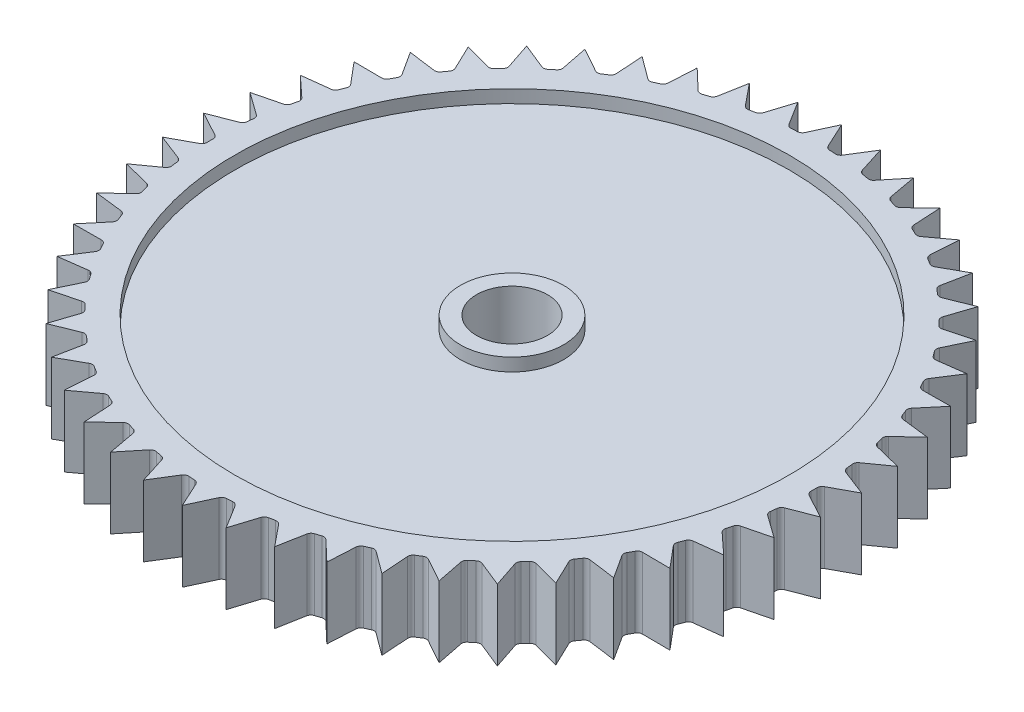
SolidWorks part; units mm, degrees
material "Acrylic (Medium-high impact)"
ref_plane "Front Plane" through (0, 0, 0) normal (0, 0, 1) x (1, 0, 0)
ref_plane "Top Plane" through (0, 0, 0) normal (0, 1, 0) x (1, 0, 0)
ref_plane "Right Plane" through (0, 0, 0) normal (1, 0, 0) x (0, 0, -1)
sketch "Sketch1" plane through (0, 0, 0) normal (0, 1, 0) x (1, 0, 0)
  line L0 (0, 0) -> (0, 28.57) construction
  line L1 (0, 0) -> (28.57, 0) construction
  line L2 (0, 0) -> (-28.57, 0) construction
  line L3 (0, 0) -> (0, -28.57) construction
  line L5 (0, 25.57) -> (-0.8983, 23.6239)
  line L7 (0, 25.57) -> (0.8983, 23.6239)
  line L12 (3.2048, 25.3684) -> (2.0696, 23.5502)
  line L13 (3.2048, 25.3684) -> (3.8521, 23.3251)
  line L14 (6.359, 24.7667) -> (5.0049, 23.1051)
  line L15 (6.359, 24.7667) -> (6.7451, 22.6583)
  line L16 (9.4129, 23.7744) -> (7.8613, 22.2957)
  line L17 (9.4129, 23.7744) -> (9.5318, 21.6343)
  line L18 (12.3184, 22.4072) -> (10.5937, 21.1346)
  line L19 (12.3184, 22.4072) -> (12.1681, 20.269)
  line L20 (15.0297, 20.6866) -> (13.1591, 19.6402)
  line L21 (15.0297, 20.6866) -> (14.6126, 18.5842)
  line L22 (17.5039, 18.6397) -> (15.5169, 17.836)
  line L23 (17.5039, 18.6397) -> (16.8265, 16.6062)
  line L24 (19.702, 16.2989) -> (17.63, 15.7506)
  line L25 (19.702, 16.2989) -> (18.7752, 14.3663)
  line L26 (21.5895, 13.7011) -> (19.465, 13.4168)
  line L27 (21.5895, 13.7011) -> (20.4277, 11.8999)
  line L28 (23.1364, 10.8872) -> (20.9931, 10.8714)
  line L29 (23.1364, 10.8872) -> (21.7581, 9.2458)
  line L30 (24.3185, 7.9016) -> (22.1901, 8.1545)
  line L31 (24.3185, 7.9016) -> (22.7453, 6.4459)
  line L33 (25.1171, 4.7913) -> (23.3738, 3.5443)
  line L34 (25.5195, 1.6056) -> (23.5209, 2.3799)
  line L35 (25.5195, 1.6056) -> (23.6337, 0.5868)
  line L36 (25.5195, -1.6056) -> (23.6337, -0.5868)
  line L37 (25.5195, -1.6056) -> (23.5209, -2.3799)
  line L38 (25.1171, -4.7913) -> (23.3738, -3.5443)
  line L39 (25.1171, -4.7913) -> (23.0372, -5.3091)
  line L40 (24.3185, -7.9016) -> (22.7453, -6.4459)
  line L41 (24.3185, -7.9016) -> (22.1901, -8.1545)
  line L42 (23.1364, -10.8872) -> (21.7581, -9.2458)
  line L43 (23.1364, -10.8872) -> (20.9931, -10.8714)
  line L44 (21.5895, -13.7011) -> (20.4277, -11.8999)
  line L45 (21.5895, -13.7011) -> (19.465, -13.4168)
  line L46 (19.702, -16.2989) -> (18.7752, -14.3663)
  line L47 (19.702, -16.2989) -> (17.63, -15.7506)
  line L48 (17.5039, -18.6397) -> (16.8265, -16.6062)
  line L49 (17.5039, -18.6397) -> (15.5169, -17.836)
  line L50 (15.0297, -20.6866) -> (14.6126, -18.5842)
  line L51 (15.0297, -20.6866) -> (13.1591, -19.6402)
  line L52 (12.3184, -22.4072) -> (12.1681, -20.269)
  line L53 (12.3184, -22.4072) -> (10.5937, -21.1346)
  line L54 (9.4129, -23.7744) -> (9.5318, -21.6343)
  line L55 (9.4129, -23.7744) -> (7.8613, -22.2957)
  line L56 (6.359, -24.7667) -> (6.7451, -22.6583)
  line L57 (6.359, -24.7667) -> (5.0049, -23.1051)
  line L58 (3.2048, -25.3684) -> (3.8521, -23.3251)
  line L59 (3.2048, -25.3684) -> (2.0696, -23.5502)
  line L60 (0, -25.57) -> (0.8983, -23.6239)
  line L61 (0, -25.57) -> (-0.8983, -23.6239)
  line L62 (-3.2048, -25.3684) -> (-2.0696, -23.5502)
  line L63 (-3.2048, -25.3684) -> (-3.8521, -23.3251)
  line L64 (-6.359, -24.7667) -> (-5.0049, -23.1051)
  line L65 (-6.359, -24.7667) -> (-6.7451, -22.6583)
  line L66 (-9.4129, -23.7744) -> (-7.8613, -22.2957)
  line L67 (-9.4129, -23.7744) -> (-9.5318, -21.6343)
  line L68 (-12.3184, -22.4072) -> (-10.5937, -21.1346)
  line L69 (-12.3184, -22.4072) -> (-12.1681, -20.269)
  line L70 (-15.0297, -20.6866) -> (-13.1591, -19.6402)
  line L71 (-15.0297, -20.6866) -> (-14.6126, -18.5842)
  line L72 (-17.5039, -18.6397) -> (-15.5169, -17.836)
  line L73 (-17.5039, -18.6397) -> (-16.8265, -16.6062)
  line L74 (-19.702, -16.2989) -> (-17.63, -15.7506)
  line L75 (-19.702, -16.2989) -> (-18.7752, -14.3663)
  line L76 (-21.5895, -13.7011) -> (-19.465, -13.4168)
  line L77 (-21.5895, -13.7011) -> (-20.4277, -11.8999)
  line L78 (-23.1364, -10.8872) -> (-20.9931, -10.8714)
  line L79 (-23.1364, -10.8872) -> (-21.7581, -9.2458)
  line L80 (-24.3185, -7.9016) -> (-22.1901, -8.1545)
  line L81 (-24.3185, -7.9016) -> (-22.7453, -6.4459)
  line L82 (-25.1171, -4.7913) -> (-23.0372, -5.3091)
  line L83 (-25.1171, -4.7913) -> (-23.3738, -3.5443)
  line L84 (-25.5195, -1.6056) -> (-23.5209, -2.3799)
  line L85 (-25.5195, -1.6056) -> (-23.6337, -0.5868)
  line L86 (-25.5195, 1.6056) -> (-23.6337, 0.5868)
  line L87 (-25.5195, 1.6056) -> (-23.5209, 2.3799)
  line L88 (-25.1171, 4.7913) -> (-23.3738, 3.5443)
  line L89 (-25.1171, 4.7913) -> (-23.0372, 5.3091)
  line L90 (-24.3185, 7.9016) -> (-22.7453, 6.4459)
  line L91 (-24.3185, 7.9016) -> (-22.1901, 8.1545)
  line L92 (-23.1364, 10.8872) -> (-21.7581, 9.2458)
  line L93 (-23.1364, 10.8872) -> (-20.9931, 10.8714)
  line L94 (-21.5895, 13.7011) -> (-20.4277, 11.8999)
  line L95 (-21.5895, 13.7011) -> (-19.465, 13.4168)
  line L96 (-19.702, 16.2989) -> (-18.7752, 14.3663)
  line L97 (-19.702, 16.2989) -> (-17.63, 15.7506)
  line L98 (-17.5039, 18.6397) -> (-16.8265, 16.6062)
  line L99 (-17.5039, 18.6397) -> (-15.5169, 17.836)
  line L100 (-15.0297, 20.6866) -> (-14.6126, 18.5842)
  line L101 (-15.0297, 20.6866) -> (-13.1591, 19.6402)
  line L102 (-12.3184, 22.4072) -> (-12.1681, 20.269)
  line L103 (-12.3184, 22.4072) -> (-10.5937, 21.1346)
  line L104 (-9.4129, 23.7744) -> (-9.5318, 21.6343)
  line L105 (-9.4129, 23.7744) -> (-7.8613, 22.2957)
  line L106 (-6.359, 24.7667) -> (-6.7451, 22.6583)
  line L107 (-6.359, 24.7667) -> (-5.0049, 23.1051)
  line L108 (-3.2048, 25.3684) -> (-3.8521, 23.3251)
  line L109 (-3.2048, 25.3684) -> (-2.0696, 23.5502)
  line L110 (25.1171, 4.7913) -> (23.0372, 5.3091) [skipped]
  line L111 (25.1171, 4.7913) -> (23.0372, 5.3091)
  arc A55 (-1.2403, 23.3921) -> (-1.7013, 23.3631) centre (0, 0) ccw
  circle A56 centre (0, 0) radius 25.57 construction
  arc A57 (0.8983, 23.6239) -> (1.2403, 23.3921) centre (1.2615, 23.7916) ccw
  arc A58 (-0.8983, 23.6239) -> (-1.2403, 23.3921) centre (-1.2615, 23.7916) cw
  arc A59 (2.0696, 23.5502) -> (1.7013, 23.3631) centre (1.7303, 23.7621) cw
  arc A60 (3.8521, 23.3251) -> (4.1623, 23.0522) centre (4.2334, 23.4459) ccw
  arc A61 (5.0049, 23.1051) -> (4.616, 22.9657) centre (4.6949, 23.3578) cw
  arc A62 (6.7451, 22.6583) -> (7.0187, 22.3488) centre (7.1386, 22.7304) ccw
  arc A63 (7.8613, 22.2957) -> (7.458, 22.2061) centre (7.5854, 22.5852) cw
  arc A64 (9.5318, 21.6343) -> (9.7644, 21.2929) centre (9.9312, 21.6565) ccw
  arc A65 (10.5937, 21.1346) -> (10.1824, 21.0962) centre (10.3562, 21.4564) cw
  arc A66 (12.1681, 20.269) -> (12.3561, 19.9012) centre (12.5671, 20.241) ccw
  arc A67 (13.1591, 19.6402) -> (12.7461, 19.6537) centre (12.9638, 19.9893) cw
  arc A68 (14.6126, 18.5842) -> (14.753, 18.1956) centre (15.0049, 18.5063) ccw
  arc A69 (15.5169, 17.836) -> (15.1089, 17.9012) centre (15.3669, 18.2069) cw
  arc A70 (16.8265, 16.6062) -> (16.9172, 16.2031) centre (17.206, 16.4798) ccw
  arc A71 (17.63, 15.7506) -> (17.2334, 15.8664) centre (17.5276, 16.1373) cw
  arc A72 (18.7752, 14.3663) -> (18.8146, 13.955) centre (19.1358, 14.1933) ccw
  arc A73 (19.465, 13.4168) -> (19.086, 13.5814) centre (19.412, 13.8133) cw
  arc A74 (20.4277, 11.8999) -> (20.4152, 11.4869) centre (20.7638, 11.6831) ccw
  arc A75 (20.9931, 10.8714) -> (20.6377, 11.0822) centre (20.9902, 11.2714) cw
  arc A76 (21.7581, 9.2458) -> (21.6939, 8.8376) centre (22.0644, 8.9885) ccw
  arc A77 (22.1901, 8.1545) -> (21.864, 8.4082) centre (22.2373, 8.5517) cw
  arc A78 (22.7453, 6.4459) -> (22.6305, 6.049) centre (23.017, 6.1523) ccw
  arc A79 (23.0372, 5.3091) -> (22.7454, 5.6016) centre (23.1338, 5.6972) cw
  arc A80 (23.3738, 3.5443) -> (23.2102, 3.1649) centre (23.6065, 3.219) ccw
  arc A81 (23.5209, 2.3799) -> (23.2681, 2.7067) centre (23.6654, 2.7529) cw
  arc A82 (23.6337, 0.5868) -> (23.4239, 0.2309) centre (23.8238, 0.2349) ccw
  arc A83 (23.6337, -0.5868) -> (23.4239, -0.2309) centre (23.8238, -0.2349) cw
  arc A84 (23.5209, -2.3799) -> (23.2681, -2.7067) centre (23.6654, -2.7529) ccw
  arc A85 (23.3738, -3.5443) -> (23.2102, -3.1649) centre (23.6065, -3.219) cw
  arc A86 (23.0372, -5.3091) -> (22.7454, -5.6016) centre (23.1338, -5.6972) ccw
  arc A87 (22.7453, -6.4459) -> (22.6305, -6.049) centre (23.017, -6.1523) cw
  arc A88 (22.1901, -8.1545) -> (21.864, -8.4082) centre (22.2373, -8.5517) ccw
  arc A89 (21.7581, -9.2458) -> (21.6939, -8.8376) centre (22.0644, -8.9885) cw
  arc A90 (20.9931, -10.8714) -> (20.6377, -11.0822) centre (20.9902, -11.2714) ccw
  arc A91 (20.4277, -11.8999) -> (20.4152, -11.4869) centre (20.7638, -11.6831) cw
  arc A92 (19.465, -13.4168) -> (19.086, -13.5814) centre (19.412, -13.8133) ccw
  arc A93 (18.7752, -14.3663) -> (18.8146, -13.955) centre (19.1358, -14.1933) cw
  arc A94 (17.63, -15.7506) -> (17.2334, -15.8664) centre (17.5276, -16.1373) ccw
  arc A95 (16.8265, -16.6062) -> (16.9172, -16.2031) centre (17.206, -16.4798) cw
  arc A96 (15.5169, -17.836) -> (15.1089, -17.9012) centre (15.3669, -18.2069) ccw
  arc A97 (14.6126, -18.5842) -> (14.753, -18.1956) centre (15.0049, -18.5063) cw
  arc A98 (13.1591, -19.6402) -> (12.7461, -19.6537) centre (12.9638, -19.9893) ccw
  arc A99 (12.1681, -20.269) -> (12.3561, -19.9012) centre (12.5671, -20.241) cw
  arc A100 (10.5937, -21.1346) -> (10.1824, -21.0962) centre (10.3562, -21.4564) ccw
  arc A101 (9.5318, -21.6343) -> (9.7644, -21.2929) centre (9.9312, -21.6565) cw
  arc A102 (7.8613, -22.2957) -> (7.458, -22.2061) centre (7.5854, -22.5852) ccw
  arc A103 (6.7451, -22.6583) -> (7.0187, -22.3488) centre (7.1386, -22.7304) cw
  arc A104 (5.0049, -23.1051) -> (4.616, -22.9657) centre (4.6949, -23.3578) ccw
  arc A105 (3.8521, -23.3251) -> (4.1623, -23.0522) centre (4.2334, -23.4459) cw
  arc A106 (2.0696, -23.5502) -> (1.7013, -23.3631) centre (1.7303, -23.7621) ccw
  arc A107 (0.8983, -23.6239) -> (1.2403, -23.3921) centre (1.2615, -23.7916) cw
  arc A108 (-0.8983, -23.6239) -> (-1.2403, -23.3921) centre (-1.2615, -23.7916) ccw
  arc A109 (-2.0696, -23.5502) -> (-1.7013, -23.3631) centre (-1.7303, -23.7621) cw
  arc A110 (-3.8521, -23.3251) -> (-4.1623, -23.0522) centre (-4.2334, -23.4459) ccw
  arc A111 (-5.0049, -23.1051) -> (-4.616, -22.9657) centre (-4.6949, -23.3578) cw
  arc A112 (-6.7451, -22.6583) -> (-7.0187, -22.3488) centre (-7.1386, -22.7304) ccw
  arc A113 (-7.8613, -22.2957) -> (-7.458, -22.2061) centre (-7.5854, -22.5852) cw
  arc A114 (-9.5318, -21.6343) -> (-9.7644, -21.2929) centre (-9.9312, -21.6565) ccw
  arc A115 (-10.5937, -21.1346) -> (-10.1824, -21.0962) centre (-10.3562, -21.4564) cw
  arc A116 (-12.1681, -20.269) -> (-12.3561, -19.9012) centre (-12.5671, -20.241) ccw
  arc A117 (-13.1591, -19.6402) -> (-12.7461, -19.6537) centre (-12.9638, -19.9893) cw
  arc A118 (-14.6126, -18.5842) -> (-14.753, -18.1956) centre (-15.0049, -18.5063) ccw
  arc A119 (-15.5169, -17.836) -> (-15.1089, -17.9012) centre (-15.3669, -18.2069) cw
  arc A120 (-16.8265, -16.6062) -> (-16.9172, -16.2031) centre (-17.206, -16.4798) ccw
  arc A121 (-17.63, -15.7506) -> (-17.2334, -15.8664) centre (-17.5276, -16.1373) cw
  arc A122 (-18.7752, -14.3663) -> (-18.8146, -13.955) centre (-19.1358, -14.1933) ccw
  arc A123 (-19.465, -13.4168) -> (-19.086, -13.5814) centre (-19.412, -13.8133) cw
  arc A124 (-20.4277, -11.8999) -> (-20.4152, -11.4869) centre (-20.7638, -11.6831) ccw
  arc A125 (-20.9931, -10.8714) -> (-20.6377, -11.0822) centre (-20.9902, -11.2714) cw
  arc A126 (-21.7581, -9.2458) -> (-21.6939, -8.8376) centre (-22.0644, -8.9885) ccw
  arc A127 (-22.1901, -8.1545) -> (-21.864, -8.4082) centre (-22.2373, -8.5517) cw
  arc A128 (-22.7453, -6.4459) -> (-22.6305, -6.049) centre (-23.017, -6.1523) ccw
  arc A129 (-23.0372, -5.3091) -> (-22.7454, -5.6016) centre (-23.1338, -5.6972) cw
  arc A130 (-23.3738, -3.5443) -> (-23.2102, -3.1649) centre (-23.6065, -3.219) ccw
  arc A131 (-23.5209, -2.3799) -> (-23.2681, -2.7067) centre (-23.6654, -2.7529) cw
  arc A132 (-23.6337, -0.5868) -> (-23.4239, -0.2309) centre (-23.8238, -0.2349) ccw
  arc A133 (-23.6337, 0.5868) -> (-23.4239, 0.2309) centre (-23.8238, 0.2349) cw
  arc A134 (-23.5209, 2.3799) -> (-23.2681, 2.7067) centre (-23.6654, 2.7529) ccw
  arc A135 (-23.3738, 3.5443) -> (-23.2102, 3.1649) centre (-23.6065, 3.219) cw
  arc A136 (-23.0372, 5.3091) -> (-22.7454, 5.6016) centre (-23.1338, 5.6972) ccw
  arc A137 (-22.7453, 6.4459) -> (-22.6305, 6.049) centre (-23.017, 6.1523) cw
  arc A138 (-22.1901, 8.1545) -> (-21.864, 8.4082) centre (-22.2373, 8.5517) ccw
  arc A139 (-21.7581, 9.2458) -> (-21.6939, 8.8376) centre (-22.0644, 8.9885) cw
  arc A140 (-20.9931, 10.8714) -> (-20.6377, 11.0822) centre (-20.9902, 11.2714) ccw
  arc A141 (-20.4277, 11.8999) -> (-20.4152, 11.4869) centre (-20.7638, 11.6831) cw
  arc A142 (-19.465, 13.4168) -> (-19.086, 13.5814) centre (-19.412, 13.8133) ccw
  arc A143 (-18.7752, 14.3663) -> (-18.8146, 13.955) centre (-19.1358, 14.1933) cw
  arc A144 (-17.63, 15.7506) -> (-17.2334, 15.8664) centre (-17.5276, 16.1373) ccw
  arc A145 (-16.8265, 16.6062) -> (-16.9172, 16.2031) centre (-17.206, 16.4798) cw
  arc A146 (-15.5169, 17.836) -> (-15.1089, 17.9012) centre (-15.3669, 18.2069) ccw
  arc A147 (-14.6126, 18.5842) -> (-14.753, 18.1956) centre (-15.0049, 18.5063) cw
  arc A148 (-13.1591, 19.6402) -> (-12.7461, 19.6537) centre (-12.9638, 19.9893) ccw
  arc A149 (-12.1681, 20.269) -> (-12.3561, 19.9012) centre (-12.5671, 20.241) cw
  arc A150 (-10.5937, 21.1346) -> (-10.1824, 21.0962) centre (-10.3562, 21.4564) ccw
  arc A151 (-9.5318, 21.6343) -> (-9.7644, 21.2929) centre (-9.9312, 21.6565) cw
  arc A152 (-7.8613, 22.2957) -> (-7.458, 22.2061) centre (-7.5854, 22.5852) ccw
  arc A153 (-6.7451, 22.6583) -> (-7.0187, 22.3488) centre (-7.1386, 22.7304) cw
  arc A154 (-5.0049, 23.1051) -> (-4.616, 22.9657) centre (-4.6949, 23.3578) ccw
  arc A155 (-3.8521, 23.3251) -> (-4.1623, 23.0522) centre (-4.2334, 23.4459) cw
  arc A156 (-2.0696, 23.5502) -> (-1.7013, 23.3631) centre (-1.7303, 23.7621) ccw
  arc A157 (-4.1623, 23.0522) -> (-4.616, 22.9657) centre (0, 0) ccw
  arc A158 (-7.0187, 22.3488) -> (-7.458, 22.2061) centre (0, 0) ccw
  arc A159 (-9.7644, 21.2929) -> (-10.1824, 21.0962) centre (0, 0) ccw
  arc A160 (1.7013, 23.3631) -> (1.2403, 23.3921) centre (0, 0) ccw
  arc A161 (4.616, 22.9657) -> (4.1623, 23.0522) centre (0, 0) ccw
  arc A162 (7.458, 22.2061) -> (7.0187, 22.3488) centre (0, 0) ccw
  arc A163 (10.1824, 21.0962) -> (9.7644, 21.2929) centre (0, 0) ccw
  arc A164 (12.7461, 19.6537) -> (12.3561, 19.9012) centre (0, 0) ccw
  arc A165 (15.1089, 17.9012) -> (14.753, 18.1956) centre (0, 0) ccw
  arc A166 (-14.753, 18.1956) -> (-15.1089, 17.9012) centre (0, 0) ccw
  arc A167 (-12.3561, 19.9012) -> (-12.7461, 19.6537) centre (0, 0) ccw
  arc A168 (-16.9172, 16.2031) -> (-17.2334, 15.8664) centre (0, 0) ccw
  arc A169 (-18.8146, 13.955) -> (-19.086, 13.5814) centre (0, 0) ccw
  arc A170 (-20.4152, 11.4869) -> (-20.6377, 11.0822) centre (0, 0) ccw
  arc A171 (-21.6939, 8.8376) -> (-21.864, 8.4082) centre (0, 0) ccw
  arc A172 (-22.6305, 6.049) -> (-22.7454, 5.6016) centre (0, 0) ccw
  arc A173 (-23.2102, 3.1649) -> (-23.2681, 2.7067) centre (0, 0) ccw
  arc A174 (-23.4239, 0.2309) -> (-23.4239, -0.2309) centre (0, 0) ccw
  arc A175 (-23.2681, -2.7067) -> (-23.2102, -3.1649) centre (0, 0) ccw
  arc A176 (-22.7454, -5.6016) -> (-22.6305, -6.049) centre (0, 0) ccw
  arc A177 (17.2334, 15.8664) -> (16.9172, 16.2031) centre (0, 0) ccw
  arc A178 (19.086, 13.5814) -> (18.8146, 13.955) centre (0, 0) ccw
  arc A179 (20.6377, 11.0822) -> (20.4152, 11.4869) centre (0, 0) ccw
  arc A180 (21.864, 8.4082) -> (21.6939, 8.8376) centre (0, 0) ccw
  arc A181 (23.2681, 2.7067) -> (23.2102, 3.1649) centre (0, 0) ccw
  arc A182 (23.4239, -0.2309) -> (23.4239, 0.2309) centre (0, 0) ccw
  arc A183 (23.2102, -3.1649) -> (23.2681, -2.7067) centre (0, 0) ccw
  arc A184 (22.6305, -6.049) -> (22.7454, -5.6016) centre (0, 0) ccw
  arc A185 (21.6939, -8.8376) -> (21.864, -8.4082) centre (0, 0) ccw
  arc A186 (20.4152, -11.4869) -> (20.6377, -11.0822) centre (0, 0) ccw
  arc A187 (18.8146, -13.955) -> (19.086, -13.5814) centre (0, 0) ccw
  arc A188 (16.9172, -16.2031) -> (17.2334, -15.8664) centre (0, 0) ccw
  arc A189 (14.753, -18.1956) -> (15.1089, -17.9012) centre (0, 0) ccw
  arc A190 (12.3561, -19.9012) -> (12.7461, -19.6537) centre (0, 0) ccw
  arc A191 (9.7644, -21.2929) -> (10.1824, -21.0962) centre (0, 0) ccw
  arc A192 (7.0187, -22.3488) -> (7.458, -22.2061) centre (0, 0) ccw
  arc A193 (4.1623, -23.0522) -> (4.616, -22.9657) centre (0, 0) ccw
  arc A194 (1.2403, -23.3921) -> (1.7013, -23.3631) centre (0, 0) ccw
  arc A195 (-1.7013, -23.3631) -> (-1.2403, -23.3921) centre (0, 0) ccw
  arc A196 (-4.616, -22.9657) -> (-4.1623, -23.0522) centre (0, 0) ccw
  arc A197 (-7.458, -22.2061) -> (-7.0187, -22.3488) centre (0, 0) ccw
  arc A198 (-10.1824, -21.0962) -> (-9.7644, -21.2929) centre (0, 0) ccw
  arc A199 (-12.7461, -19.6537) -> (-12.3561, -19.9012) centre (0, 0) ccw
  arc A200 (-15.1089, -17.9012) -> (-14.753, -18.1956) centre (0, 0) ccw
  arc A201 (-17.2334, -15.8664) -> (-16.9172, -16.2031) centre (0, 0) ccw
  arc A202 (-19.086, -13.5814) -> (-18.8146, -13.955) centre (0, 0) ccw
  arc A203 (-20.6377, -11.0822) -> (-20.4152, -11.4869) centre (0, 0) ccw
  arc A204 (-21.864, -8.4082) -> (-21.6939, -8.8376) centre (0, 0) ccw
  arc A205 (22.7454, 5.6016) -> (22.6305, 6.049) centre (0, 0) ccw
  point P11 (1, 23.4036)
  point P14 (-1, 23.4036)
  point P361 (0, 0)
  dimension "D1" = 46.85
  dimension "D2" = 51.14
  dimension "D6" = 0.4
  dimension "D3" = 28.57
  dimension "D4" = 2
  dimension "D5" = 24.778
extrude "Boss-Extrude1" add sketch "Sketch1" along normal blind 5.5
sketch "Sketch2" plane through (0, 5.5, 0) normal (0, 1, 0) x (1, 0, 0)
  circle A0 centre (0, 0) radius 2.75
  dimension "D1" = 5.5
extrude "Cut-Extrude1" cut sketch "Sketch2" against normal through all
sketch "Sketch3" plane through (0, 5.5, 0) normal (0, 1, 0) x (1, 0, 0)
  circle A0 centre (0, 0) radius 4
  circle A1 centre (0, 0) radius 21.5
  dimension "D1" = 43
  dimension "D2" = 8
extrude "Cut-Extrude2" cut sketch "Sketch3" against normal blind 1
sketch "Sketch4" plane through (0, 0, 0) normal (0, -1, 0) x (1, 0, 0)
  circle A0 centre (0, 0) radius 4
  circle A1 centre (0, 0) radius 21.5
  dimension "D1" = 43
  dimension "D2" = 8
extrude "Cut-Extrude4" cut sketch "Sketch4" against normal blind 1 contours A1 | A0
sketch "Sketch5" plane through (0, 5.5, 0) normal (0, 1, 0) x (1, 0, 0)
  circle A0 centre (0, 0) radius 25
  dimension "D1" = 50
